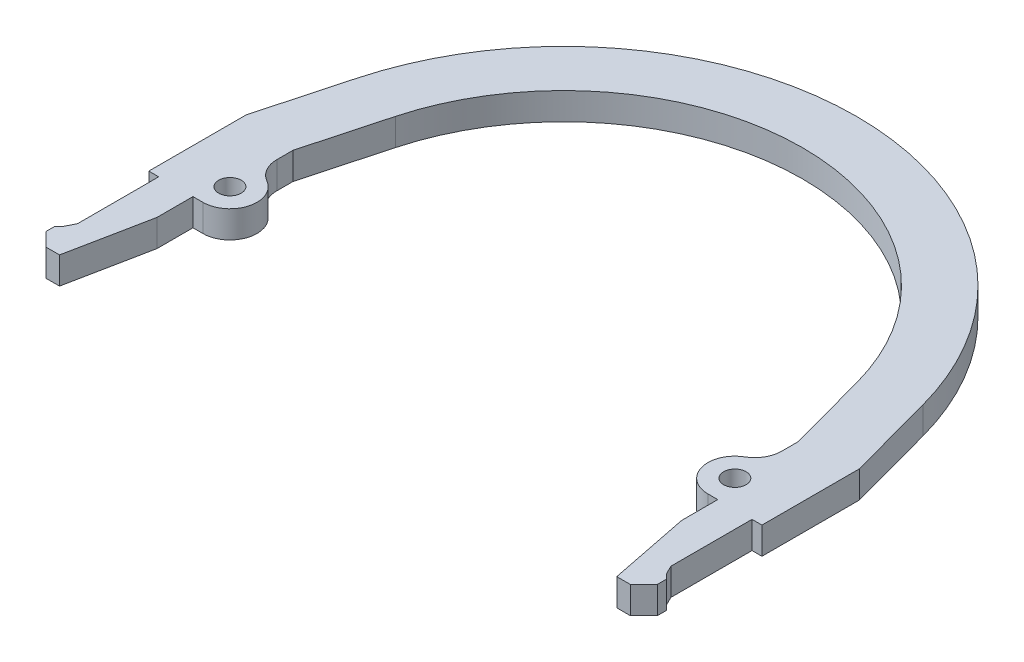
SolidWorks part; units mm, degrees
material "Lasercut ABS"
ref_plane "Front Plane" through (0, 0, 0) normal (0, 0, 1) x (1, 0, 0)
ref_plane "Top Plane" through (0, 0, 0) normal (0, 1, 0) x (1, 0, 0)
ref_plane "Right Plane" through (0, 0, 0) normal (1, 0, 0) x (0, 0, -1)
sketch "Sketch1" plane through (0, 0, 0) normal (0, 1, 0) x (1, 0, 0)
  line L0 (29.1, -16) -> (29.1, -12)
  line L1 (32.9, -21) -> (32.9, -12)
  line L2 (29.1, -12) -> (28, -12)
  line L3 (29.1, -16) -> (30.9, -25)
  line L4 (30.9, -25) -> (32.4, -25)
  line L5 (32.4, -25) -> (33.9, -23.5)
  line L6 (33.9, -23.5) -> (33.9, -22.5)
  line L7 (33.9, -22.5) -> (33.4, -22)
  line L8 (33.4, -22) -> (32.9, -21)
  line L9 (32.9, -12) -> (34, -12)
  line L10 (0, 32.5) -> (0, 26.5)
  line L18 (28, -12) -> (28, -2)
  line L19 (0, 0) -> (0, -23.7709) construction
  line L25 (34, -12) -> (34, -1.2007)
  line L26 (28, -2) -> (25.5759, 6.9372)
  line L27 (34, -1.2007) -> (31.3666, 8.5079)
  arc A1 (0, 26.5) -> (25.5759, 6.9372) centre (0, 0) cw
  arc A2 (0, 32.5) -> (31.3666, 8.5079) centre (0, 0) cw
  dimension "D1" = 26.5
  dimension "D9" = 6
  dimension "D2" = 0.5
  dimension "D3" = 13
  dimension "D4" = 28
  dimension "D5" = 6
  dimension "D6" = 12
  dimension "D7" = 3.8
  dimension "D8" = 4
  dimension "D10" = 1.5
  dimension "D11" = 1.5
  dimension "D12" = 1.5
  dimension "D13" = 1
  dimension "D14" = 0.5
  dimension "D15" = 1
  dimension "D16" = 10
extrude "Boss-Extrude1" add sketch "Sketch1" along normal blind 3
sketch "Sketch3" plane through (0, 0, 0) normal (0, 1, 0) x (1, 0, 0)
  line L0 (28, -2) -> (28, -12) construction
  line L1 (28, -12) -> (29.1, -12) construction
  line L2 (28, -6) -> (28, -12)
  arc A0 (28, -12) -> (28, -6) centre (28, -9) cw
  dimension "D1" = 3
extrude "Boss-Extrude2" add sketch "Sketch3" along normal up to surface (3 mm away) up to face at (28.048, 3, 7.1833)
fillet "Fillet1" radius 3 1 edges at (28, 1.5, 6)
sketch "Sketch4" plane through (0, 3, 0) normal (0, 1, 0) x (1, 0, 0)
  circle A0 centre (28, -9) radius 1.25
  arc A1 (26.5, -6.4019) -> (28, -12) centre (28, -9) ccw construction
  dimension "D1" = 2.5
extrude "Cut-Extrude1" cut sketch "Sketch4" against normal through all contours A0
mirror "Mirror1" about plane through (0, 0, 0) normal (1, 0, 0) of bodies 104 101
sketch "Sketch2" plane through (0, 3, 0) normal (0, 1, 0) x (1, 0, 0)
  arc A0 (-12.5, 25.0549) -> (12.5, 25.0549) centre (0, 0) cw construction
  arc A1 (31.3666, 8.5079) -> (-31.3666, 8.5079) centre (0, 0) ccw construction
  text T0 "E5 ONO V2" font "1CamBam_Stick_3" height 2.5
  dimension "D1" = 28
  dimension "D2" = 25
